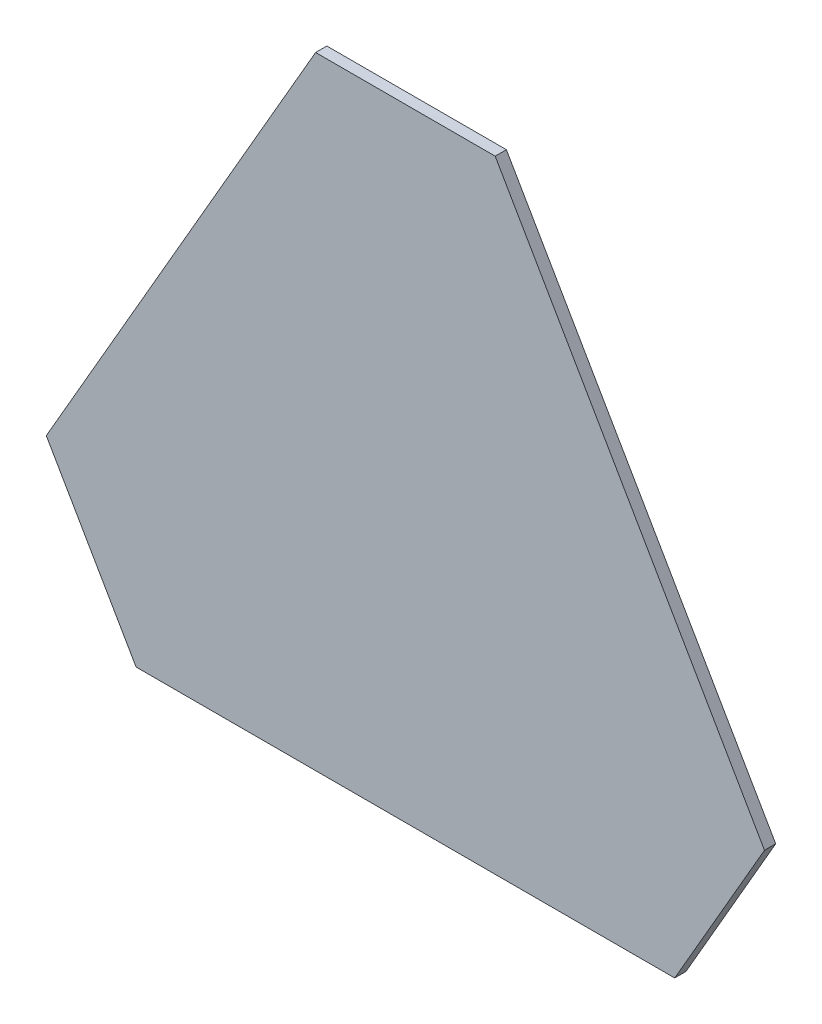
SolidWorks part; units mm, degrees
ref_plane "Front Plane" through (0, 0, 0) normal (0, 0, 1) x (1, 0, 0)
ref_plane "Top Plane" through (0, 0, 0) normal (0, 1, 0) x (1, 0, 0)
ref_plane "Right Plane" through (0, 0, 0) normal (1, 0, 0) x (0, 0, -1)
sketch "Sketch1" plane through (0, 0, 0) normal (0, 0, 1) x (1, 0, 0)
  line L0 (0, 0) -> (240, 0)
  line L1 (240, 0) -> (280, 69.282)
  line L2 (280, 69.282) -> (160, 277.1281)
  line L3 (160, 277.1281) -> (80, 277.1281)
  line L4 (80, 277.1281) -> (-40, 69.282)
  line L5 (-40, 69.282) -> (0, 0)
  dimension "D1" = 240
  dimension "D2" = 80
  dimension "D3" = 120
  dimension "D4" = 120
  dimension "D5" = 120
extrude "Boss-Extrude1" add sketch "Sketch1" along normal blind 5
sketch "Sketch2" plane through (0, 0, 5) normal (0, 0, 1) x (1, 0, 0)
  line L0 (-20, 34.641) -> (220, 173.2051)
  line L1 (-40, 69.282) -> (0, 0) construction
  line L2 (280, 69.282) -> (160, 277.1281) construction
  line L3 (260, 34.641) -> (20, 173.2051)
  line L4 (240, 0) -> (280, 69.282) construction
  line L5 (80, 277.1281) -> (-40, 69.282) construction
  line L6 (120, 0) -> (120, 277.1281)
  line L7 (0, 0) -> (240, 0) construction
  line L8 (160, 277.1281) -> (80, 277.1281) construction
